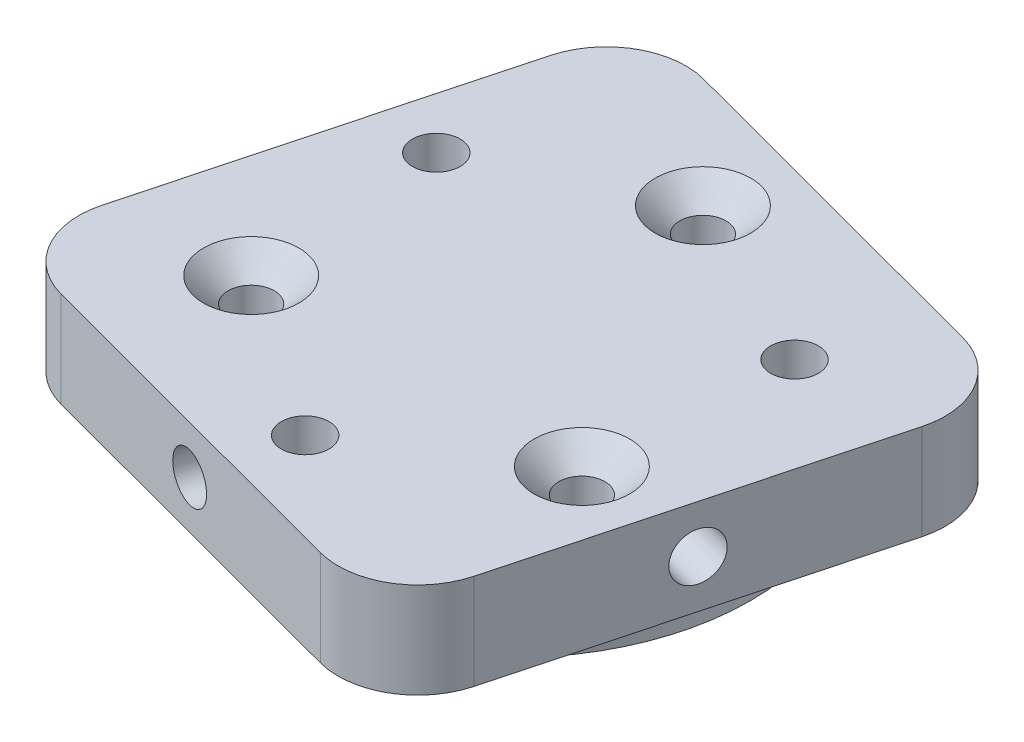
SolidWorks part; units mm, degrees
material "6061 合金"
ref_plane "前视基准面" through (0, 0, 0) normal (0, 0, 1) x (1, 0, 0)
ref_plane "上视基准面" through (0, 0, 0) normal (0, 1, 0) x (1, 0, 0)
ref_plane "右视基准面" through (0, 0, 0) normal (1, 0, 0) x (0, 0, -1)
sketch "草图1" plane through (0, 0, 0) normal (0, 1, 0) x (1, 0, 0)
  line L0 (0, 0) -> (0, 33.3478) construction
  line L1 (0, 0) -> (11.2563, 0) construction
  line L2 (-10.3923, -6) -> (0, 0) construction
  line L3 (0, 0) -> (10.3923, -6) construction
  line L4 (0, 0) -> (-11.2583, 6.5) construction
  line L5 (11.2583, 6.5) -> (0, 0) construction
  circle A0 centre (0, 0) radius 15
  circle A1 centre (0, 12) radius 1.45
  circle A2 centre (0, 0) radius 12 construction
  circle A3 centre (-10.3923, -6) radius 1.45
  circle A4 centre (10.3923, -6) radius 1.45
  circle A5 centre (0, 0) radius 13 construction
  circle A6 centre (-11.2583, 6.5) radius 1.5
  circle A7 centre (0, -13) radius 1.5
  circle A8 centre (11.2583, 6.5) radius 1.5
  dimension "D1" = 30
  dimension "D2" = 24
  dimension "D3" = 2.9
  dimension "D6" = 26
  dimension "D8" = 3
  dimension "D4" = 120
  dimension "D5" = 120
  dimension "D7" = 60
  dimension "D9" = 60
extrude "凸台-拉伸1" add sketch "草图1" along normal blind 8
sketch "草图2" plane through (0, 8, 0) normal (0, 1, 0) x (1, 0, 0)
  line L0 (0, 17.3205) -> (0, 0) construction
  line L1 (0, 17.3205) -> (-15, 8.6603) construction
  line L2 (-15, 8.6603) -> (-15, -8.6603) construction
  line L3 (-15, -8.6603) -> (0, -17.3205) construction
  line L4 (0, -17.3205) -> (15, -8.6603) construction
  line L5 (15, -8.6603) -> (15, 8.6603) construction
  line L6 (15, 8.6603) -> (0, 17.3205) construction
  line L7 (-6.8597, 18.9062) -> (15.3635, 12.9793)
  line L8 (-12.9793, 15.3635) -> (-18.9062, -6.8597)
  line L9 (18.9062, 6.8597) -> (12.9793, -15.3635)
  line L10 (-15.3635, -12.9793) -> (6.8597, -18.9062)
  line L11 (-11.6908, 20.1947) -> (11.6908, -20.1947) construction
  line L12 (20.1947, 11.6908) -> (-20.1947, -11.6908) construction
  line L13 (0, 0) -> (-4.2519, -15.9427) construction
  line L14 (0, 0) -> (-15.9427, 4.2519) construction
  circle A0 centre (0, 0) radius 15 construction
  circle A1 centre (0, 12) radius 1.45
  circle A2 centre (0, 12) radius 1.45 construction
  circle A3 centre (-11.2583, 6.5) radius 1.5
  circle A4 centre (-11.2583, 6.5) radius 1.5 construction
  circle A5 centre (11.2583, 6.5) radius 1.5
  circle A6 centre (11.2583, 6.5) radius 1.5 construction
  circle A7 centre (-10.3923, -6) radius 1.45
  circle A8 centre (-10.3923, -6) radius 1.45 construction
  circle A9 centre (0, -13) radius 1.5
  circle A10 centre (0, -13) radius 1.5 construction
  circle A11 centre (10.3923, -6) radius 1.45
  circle A12 centre (10.3923, -6) radius 1.45 construction
  arc A13 (12.9793, -15.3635) -> (6.8597, -18.9062) centre (8.1481, -14.0751) cw
  arc A14 (15.3635, 12.9793) -> (18.9062, 6.8597) centre (14.0751, 8.1481) cw
  arc A15 (-18.9062, -6.8597) -> (-15.3635, -12.9793) centre (-14.0751, -8.1481) ccw
  arc A16 (-12.9793, 15.3635) -> (-6.8597, 18.9062) centre (-8.1481, 14.0751) cw
  dimension "D1" = 30
  dimension "D2" = 5
  dimension "D3" = 33
  dimension "D4" = 3.35
extrude "凸台-拉伸2" add sketch "草图2" against normal blind 6
chamfer "倒角1" distance 1.55 angle 45 3 edges at (10.3923, 8, 7.45) (-10.3923, 8, 7.45) (0, 8, -10.55)
sketch "草图3" plane through (-15.9427, 0, -4.2519) normal (-0.9662, 0, -0.2577) x (-0.2577, 0, 0.9662)
  line L0 (0, 5) -> (0, 8) construction
  line L1 (-11.5, 8) -> (11.5, 8) construction
  circle A0 centre (0, 5) radius 1.5
  dimension "D2" = 3
  dimension "D1" = 3
extrude "切除-拉伸1" cut sketch "草图3" against normal through all contours A0
sketch "草图4" plane through (4.2519, 0, -15.9427) normal (0.2577, 0, -0.9662) x (-0.9662, 0, -0.2577)
  line L0 (0.0923, 5) -> (0.0923, 8) construction
  line L1 (-11.5, 8) -> (11.5, 8) construction
  circle A0 centre (0.0923, 5) radius 1.5
  dimension "D2" = 3
  dimension "D1" = 3
extrude "切除-拉伸2" cut sketch "草图4" against normal through all
